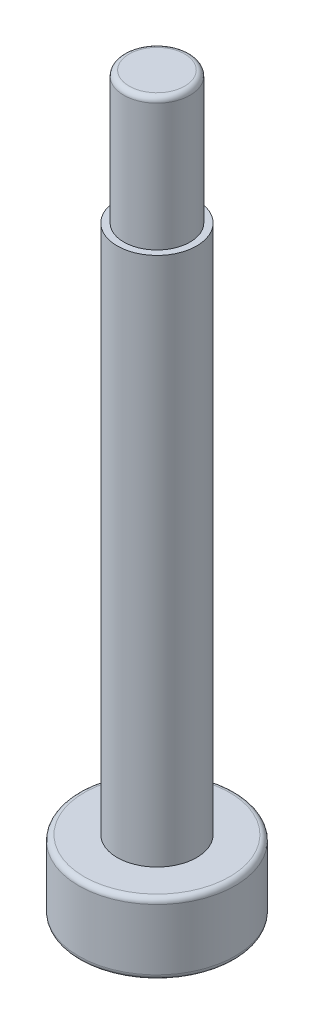
SolidWorks part; units mm, degrees
ref_plane "前视基准面" through (0, 0, 0) normal (0, 0, 1) x (1, 0, 0)
ref_plane "上视基准面" through (0, 0, 0) normal (0, 1, 0) x (1, 0, 0)
ref_plane "右视基准面" through (0, 0, 0) normal (1, 0, 0) x (0, 0, -1)
sketch "草图1" plane through (0, 0, 0) normal (0, 1, 0) x (1, 0, 0)
  circle A0 centre (0, 0) radius 2.95
  dimension "D1" = 5.9
extrude "凸台-拉伸1" add sketch "草图1" along normal blind 2.7
sketch "草图2" plane through (0, 2.7, 0) normal (0, 1, 0) x (1, 0, 0)
  circle A0 centre (0, 0) radius 1.5
  dimension "D1" = 3
extrude "凸台-拉伸2" add sketch "草图2" along normal blind 20
sketch "草图3" plane through (0, 22.7, 0) normal (0, 1, 0) x (1, 0, 0)
  circle A0 centre (0, 0) radius 1.25
  dimension "D1" = 2.5
extrude "凸台-拉伸3" add sketch "草图3" along normal blind 5
sketch "草图4" plane through (0, 0, 0) normal (0, -1, 0) x (1, 0, 0)
  line L1 (2.2473, -0.532) -> (1.5844, 1.6802)
  line L2 (1.5844, 1.6802) -> (-0.6629, 2.2122)
  line L3 (-0.6629, 2.2122) -> (-2.2473, 0.532)
  line L4 (-2.2473, 0.532) -> (-1.5844, -1.6802)
  line L5 (-1.5844, -1.6802) -> (0.6629, -2.2122)
  line L6 (0.6629, -2.2122) -> (2.2473, -0.532)
  circle A0 centre (0, 0) radius 2 construction
  dimension "D1" = 4
extrude "切除-拉伸1" cut sketch "草图4" against normal blind 2
fillet "圆角1" radius 0.2 3 edges at (0, 0, 2.95) (0, 2.7, 2.95) (0, 27.7, 1.25)
